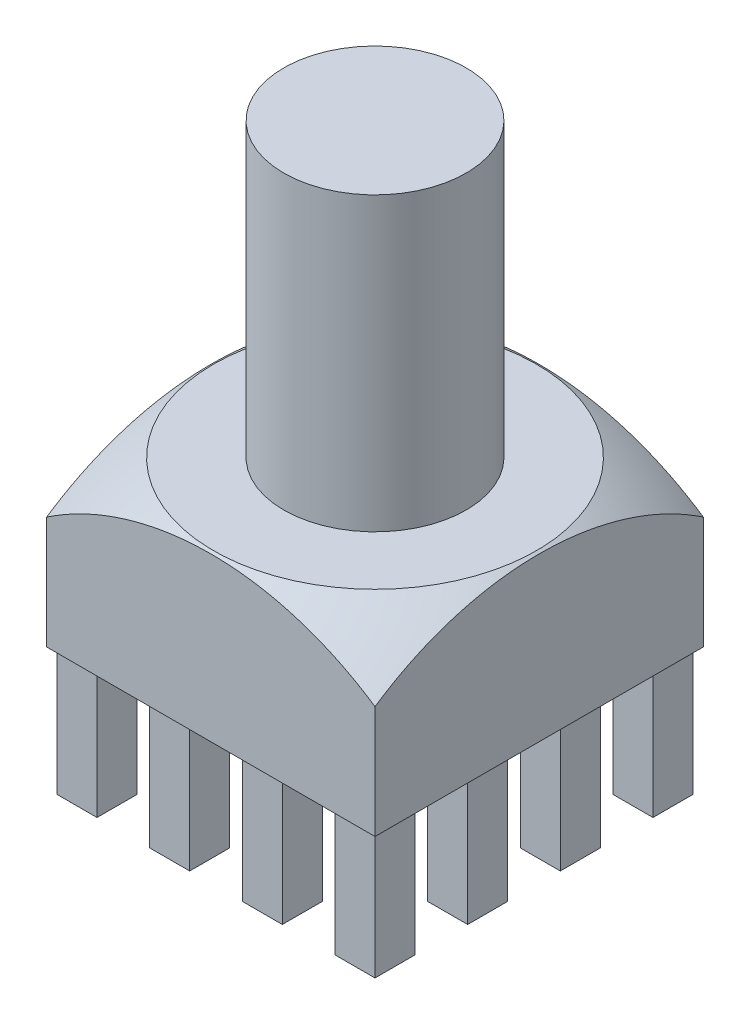
SolidWorks part; units mm, degrees
ref_plane "Front Plane" through (0, 0, 0) normal (0, 0, 1) x (1, 0, 0)
ref_plane "Top Plane" through (0, 0, 0) normal (0, 1, 0) x (1, 0, 0)
ref_plane "Right Plane" through (0, 0, 0) normal (1, 0, 0) x (0, 0, -1)
sketch "Sketch1" plane through (0, 0, 0) normal (0, 1, 0) x (1, 0, 0)
  line L1 (-4.5, 4.5) -> (4.5, 4.5)
  line L2 (-4.5, 4.5) -> (-4.5, -4.5)
  line L3 (-4.5, -4.5) -> (4.5, -4.5)
  line L4 (4.5, 4.5) -> (4.5, -4.5)
  line L5 (-4.5, 4.5) -> (4.5, -4.5) construction
  line L6 (-4.5, -4.5) -> (4.5, 4.5) construction
  point P0 (0, 0)
  dimension "D1" = 9
extrude "Boss-Extrude1" add sketch "Sketch1" along normal blind 4.5
sketch "Sketch3" plane through (0, 0, 0) normal (0, -1, 0) x (1, 0, 0)
  line L0 (0, -4.5) -> (0, 4.5) construction
  line L1 (4.5, -4.5) -> (-4.5, -4.5) construction
  line L2 (-4.5, 4.5) -> (4.5, 4.5) construction
  line L4 (-4.3585, 4.3585) -> (-3.2615, 4.3585)
  line L5 (-4.3585, 4.3585) -> (-4.3585, 3.2615)
  line L6 (-4.3585, 3.2615) -> (-3.2615, 3.2615)
  line L7 (-3.2615, 4.3585) -> (-3.2615, 3.2615)
  line L10 (-3.81, 3.2615) -> (-3.81, 4.3585) construction
  line L11 (-3.2615, 3.81) -> (-4.3585, 3.81) construction
  dimension "D1" = 3.81
  dimension "D2" = 3.81
extrude "Boss-Extrude3" add sketch "Sketch3" along normal blind 3.5
pattern_linear "LPattern1" count 4 spacing 2.54 along (1, 0, 0) count 4 spacing 2.54 along (0, 0, -1) of "Boss-Extrude3"
sketch "Sketch4" plane through (0, 4.5, 0) normal (0, 1, 0) x (1, 0, 0)
  circle A0 centre (0, 0) radius 2.5
  dimension "D1" = 5
extrude "Boss-Extrude4" add sketch "Sketch4" along normal blind 8
ref_plane "Plane1" through (0, 0, 0) normal (0.7071, 0, -0.7071) x (-0.7071, 0, -0.7071)
sketch "Sketch6" plane through (0, 0, 0) normal (0.7071, 0, -0.7071) x (-0.7071, 0, -0.7071)
  line L0 (0, 4.5) -> (0, -3.5833) construction
  line L1 (-8.778, -0.774) -> (-8.778, 5.7889)
  line L2 (-8.778, 5.7889) -> (-4.4278, 5.7889)
  line L4 (-6.364, 4.5) -> (0, 4.5) construction
  line L5 (-4.4278, 4.5) -> (-4.4278, 5.7889)
  arc A0 (-4.4278, 4.5) -> (-8.778, -0.774) centre (0, -3.5833) ccw
revolve "Cut-Revolve2" cut sketch "Sketch6" angle 360 about L0
